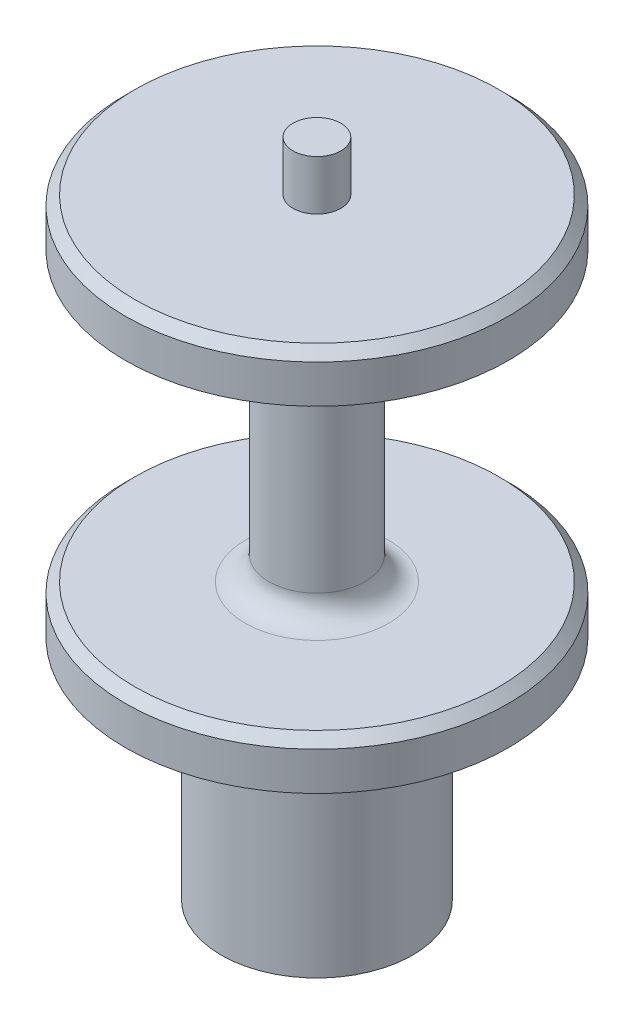
SolidWorks part; units mm, degrees
material "6061 Alloy"
ref_plane "Front Plane" through (0, 0, 0) normal (0, 0, 1) x (1, 0, 0)
ref_plane "Top Plane" through (0, 0, 0) normal (0, 1, 0) x (1, 0, 0)
ref_plane "Right Plane" through (0, 0, 0) normal (1, 0, 0) x (0, 0, -1)
sketch "Sketch1" plane through (0, 0, 0) normal (0, 1, 0) x (1, 0, 0)
  circle A0 centre (0, 0) radius 12.7
  dimension "D1" = 25.4
extrude "Boss-Extrude1" add sketch "Sketch1" along normal blind 30.1625
sketch "Sketch4" plane through (0, 30.1625, 0) normal (0, 1, 0) x (1, 0, 0)
  circle A0 centre (0, 0) radius 25.4
  dimension "D1" = 50.8
extrude "Boss-Extrude2" add sketch "Sketch4" along normal blind 50.8 contours A0
sketch "Sketch2" plane through (0, 0, 0) normal (0, -1, 0) x (1, 0, 0)
  line L0 (-8.777, 1.1225) -> (-1.1225, 8.777)
  line L1 (-5.4125, -7) -> (5.4125, -7)
  line L2 (-7, -5.4125) -> (-7, 5.4125)
  line L3 (-5.4125, 7) -> (5.4125, 7)
  line L4 (7, -5.4125) -> (7, 5.4125)
  line L5 (-7, -7) -> (7, 7) construction
  line L6 (-7, 7) -> (7, -7) construction
  line L7 (-8.777, -1.1225) -> (-1.1225, -8.777)
  line L8 (1.1225, 8.777) -> (8.777, 1.1225)
  line L9 (1.1225, -8.777) -> (8.777, -1.1225)
  line L10 (-9.8995, 0) -> (9.8995, 0) construction
  line L11 (0, 9.8995) -> (0, -9.8995) construction
  circle A0 centre (0, 0) radius 9 construction
  arc A1 (-8.777, 1.1225) -> (-8.777, -1.1225) centre (-7.6544, 0) ccw
  arc A2 (-7, -5.4125) -> (-5.4125, -7) centre (-5.4125, -5.4125) ccw
  arc A3 (-1.1225, -8.777) -> (1.1225, -8.777) centre (0, -7.6544) ccw
  arc A4 (5.4125, -7) -> (7, -5.4125) centre (5.4125, -5.4125) ccw
  arc A5 (8.777, -1.1225) -> (8.777, 1.1225) centre (7.6544, 0) ccw
  arc A6 (7, 5.4125) -> (5.4125, 7) centre (5.4125, 5.4125) ccw
  arc A7 (1.1225, 8.777) -> (-1.1225, 8.777) centre (0, 7.6544) ccw
  arc A8 (-5.4125, 7) -> (-7, 5.4125) centre (-5.4125, 5.4125) ccw
  point P0 (0, 0)
  point P7 (0, 0)
  dimension "D2" = 18
  dimension "D3" = 1.5875
  dimension "D1" = 14
extrude "Cut-Extrude1" cut sketch "Sketch2" against normal blind 11.176 contours L0 A1 L7 L2 | L1 L9 L4 L8 L3 L0 L2 L7 | L3 A8 L2 L0 | L8 A7 L0 L3 | L4 A6 L3 L8 | L9 A5 L8 L4 | L1 A4 L4 L9 | L7 A3 L9 L1 | L2 A2 L1 L7
sketch "Sketch3" plane through (0, 11.176, 0) normal (0, -1, 0) x (1, 0, 0)
  circle A0 centre (0, 0) radius 6
  dimension "D1" = 12
extrude "Cut-Extrude2" cut sketch "Sketch3" against normal blind 8
sketch "Sketch5" plane through (0, 80.9625, 0) normal (0, 1, 0) x (1, 0, 0)
  circle A0 centre (0, 0) radius 3.175
  dimension "D1" = 6.35
extrude "Boss-Extrude3" add sketch "Sketch5" along normal blind 6.604
hole_wizard "#8-32 Tapped Hole1" [suppressed] positions "Sketch6" profile "Sketch8" tap size "#8-32" standard "ANSI Inch"
sketch "Sketch6" plane through (0, 87.5665, 0) normal (0, 1, 0) x (1, 0, 0)
  point P0 (0, 0)
sketch "Sketch8" plane through (0, 87.5665, 0) normal (1, 0, 0) x (0, 0, 1)
  line L0 (0, 0) -> (0, 87.5665)
  line L1 (0, 87.5665) -> (1.7272, 87.5665)
  line L2 (1.7272, 87.5665) -> (1.7272, 0)
  line L5 (1.7272, 0) -> (0, 0)
  line L11 (0, -6.35) -> (0, 107.95) construction
  dimension "Thru Tap Drill Dia." = 3.4544
  dimension "Thru Tap Drill Depth" = 87.5665
cosmetic thread "Hole Thread1" [suppressed] parameters "D2"=4.1656
sketch "Sketch9" plane through (0, 80.9625, 0) normal (0, 1, 0) x (1, 0, 0)
  circle A0 centre (0, 0) radius 25.4 construction
  circle A1 centre (0, 0) radius 25.4
  circle A2 centre (0, 0) radius 6.35
  dimension "D1" = 12.7
extrude "Cut-Extrude3" cut sketch "Sketch9" against normal blind 38.1 from offset 6.35 offset against normal yes
fillet "Fillet1" radius 3.175 2 edges at (0, 74.6125, 6.35) (0, 36.5125, 6.35)
chamfer "Chamfer1" distance 1.27 angle 45 2 edges at (0, 36.5125, 25.4) (0, 80.9625, 25.4)
